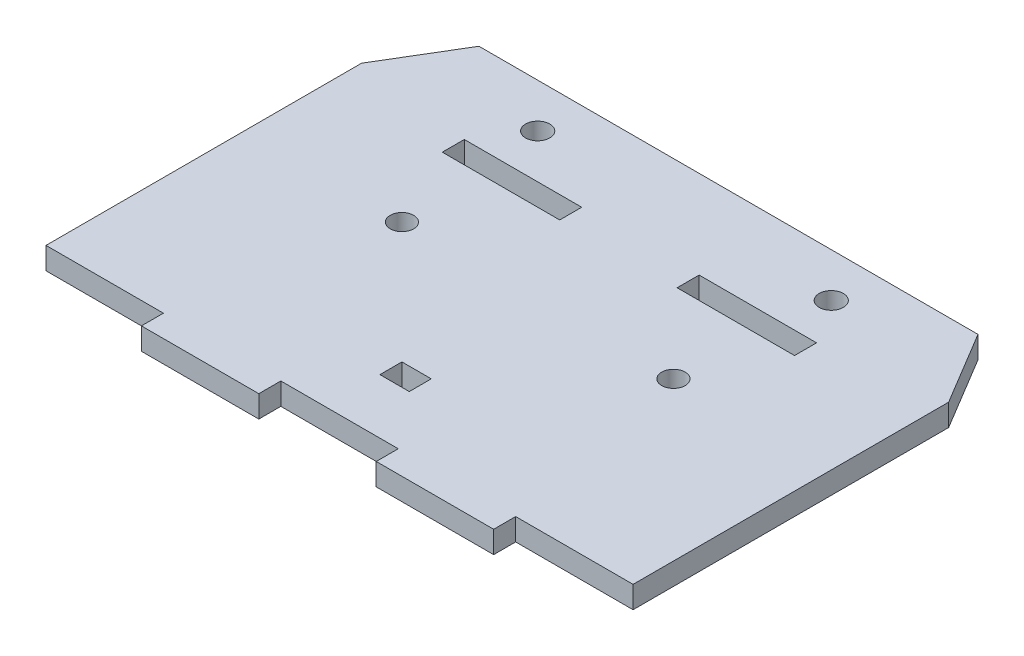
SolidWorks part; units mm, degrees
ref_plane "Ön Düzlem" through (0, 0, 0) normal (0, 0, 1) x (1, 0, 0)
ref_plane "Üst Düzlem" through (0, 0, 0) normal (0, 1, 0) x (1, 0, 0)
ref_plane "Sağ Düzlem" through (0, 0, 0) normal (1, 0, 0) x (0, 0, -1)
sketch "Sketch1" plane through (0, 0, 0) normal (0, 1, 0) x (1, 0, 0)
  line L0 (-40, 37) -> (-34, 47)
  line L1 (-34, 47) -> (34, 47)
  line L2 (-40, 37) -> (-40, -6)
  line L3 (-24, -9) -> (-8, -9)
  line L4 (40, 37) -> (40, -6)
  line L7 (34, 47) -> (40, 37)
  line L9 (-40, -6) -> (-24, -6)
  line L10 (-24, -6) -> (-24, -9)
  line L11 (-8, -9) -> (-8, -6)
  line L12 (-8, -6) -> (8, -6)
  line L13 (8, -6) -> (8, -9)
  line L14 (8, -9) -> (24, -9)
  line L15 (24, -9) -> (24, -6)
  line L16 (24, -6) -> (40, -6)
  circle A0 centre (-20, 41) radius 1.65
  circle A1 centre (20, 41.0031) radius 1.65
  point P0 (0, 0)
  dimension "D1" = 20
  dimension "D2" = 43
  dimension "D3" = 6
extrude "Boss-Extrude1" add sketch "Sketch1" along normal blind 3
sketch "Sketch2" plane through (0, 3, 0) normal (0, 1, 0) x (1, 0, 0)
  line L0 (-24, -9) -> (-8, -9) construction
  line L1 (-20, 35) -> (-8, 35) construction
  line L2 (0, 21) -> (0, 3) construction
  line L3 (-20, 35) -> (-24, 35) construction
  line L5 (0, -6) -> (0, 21) construction
  line L6 (-8, -6) -> (8, -6) construction
  line L7 (0, 21) -> (-18.5, 21) construction
  line L8 (0, 21) -> (18.5, 21) construction
  line L9 (-2, 4.5) -> (2, 4.5)
  line L10 (-24, 35) -> (-24, 32)
  line L11 (-24, 32) -> (-8, 32)
  line L12 (-8, 32) -> (-8, 35)
  line L13 (-8, 35) -> (-24, 35)
  line L14 (8, 35) -> (24, 35) construction
  line L15 (8, 32) -> (8, 35)
  line L16 (8, 35) -> (24, 35)
  line L17 (24, 35) -> (24, 32)
  line L18 (24, 32) -> (8, 32)
  line L19 (-2, 4.5) -> (-2, 1.5)
  line L20 (-2, 1.5) -> (2, 1.5)
  line L21 (2, 4.5) -> (2, 1.5)
  line L22 (-2, 4.5) -> (2, 1.5) construction
  line L23 (-2, 1.5) -> (2, 4.5) construction
  circle A0 centre (-18.5, 21) radius 1.6
  circle A1 centre (18.5, 21) radius 1.6
  dimension "D1" = 30
  dimension "D2" = 3
  dimension "D3" = 4
extrude "Cut-Extrude1" cut sketch "Sketch2" against normal through all
